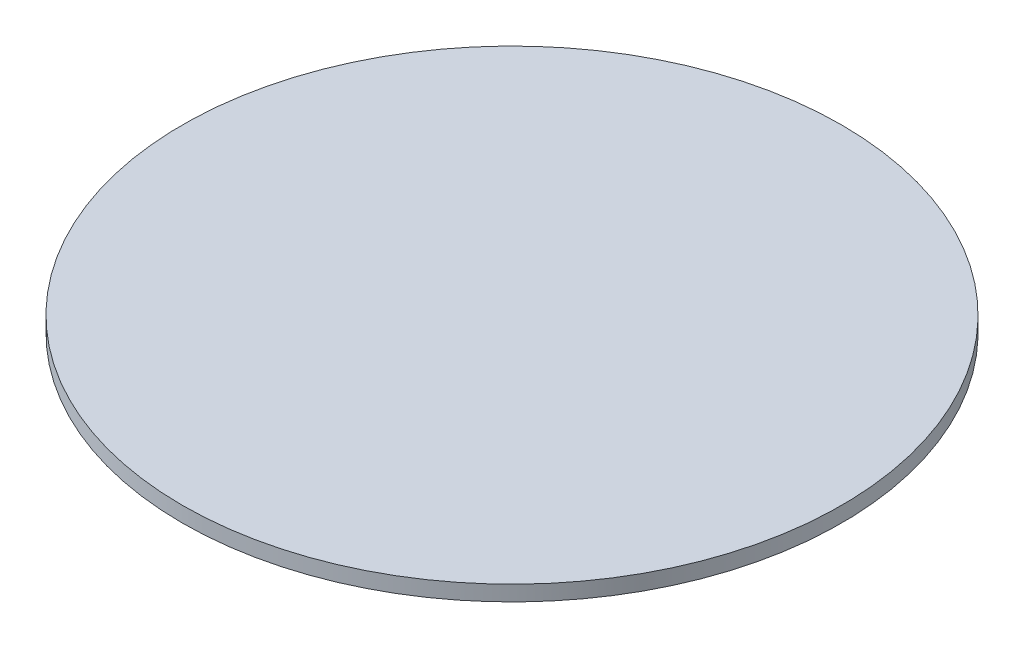
SolidWorks part; units mm, degrees
ref_plane "Front Plane" through (0, 0, 0) normal (0, 0, 1) x (1, 0, 0)
ref_plane "Top Plane" through (0, 0, 0) normal (0, 1, 0) x (1, 0, 0)
ref_plane "Right Plane" through (0, 0, 0) normal (1, 0, 0) x (0, 0, -1)
sketch "Sketch2" plane through (0, 0, 0) normal (0, 1, 0) x (1, 0, 0)
  circle A0 centre (0, 0) radius 150
extrude "Boss-Extrude8" add sketch "Sketch2" along normal blind 7
